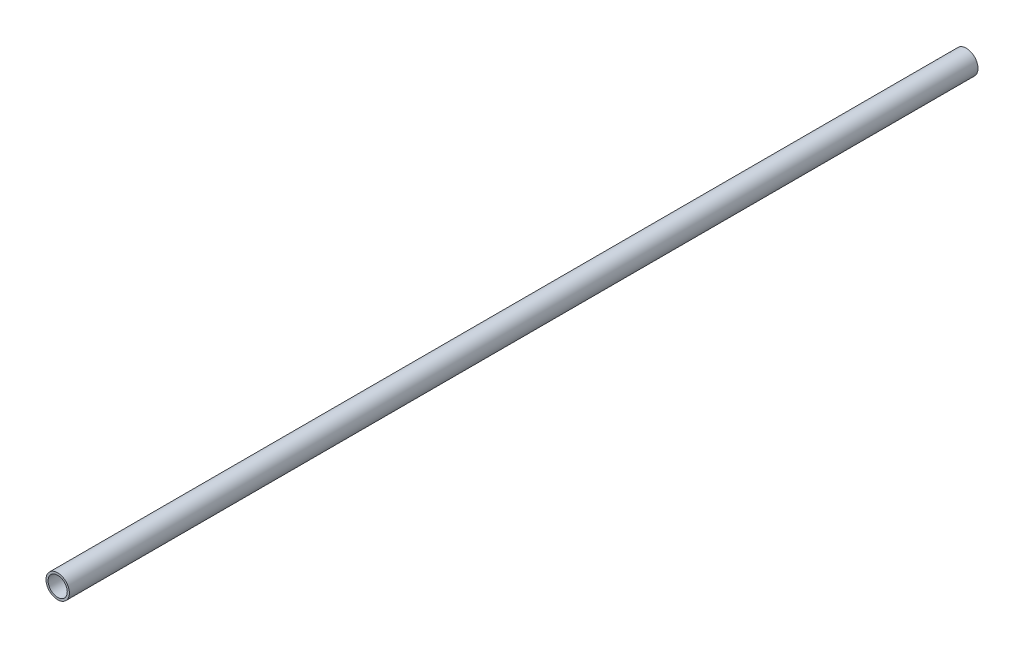
SolidWorks part; units mm, degrees
ref_plane "Front" through (0, 0, 0) normal (0, 0, 1) x (1, 0, 0)
ref_plane "Top" through (0, 0, 0) normal (0, 1, 0) x (1, 0, 0)
ref_plane "Side" through (0, 0, 0) normal (1, 0, 0) x (0, 0, -1)
sketch "PipeSketch" plane through (0, 0, 0) normal (0, 0, 1) x (1, 0, 0)
  circle A0 centre (0, 0) radius 70.612
  circle A1 centre (0, 0) radius 57.912
  dimension "OuterDiameter" = 141.224
  dimension "InnerDiameter" = 115.824
extrude "Extrusion" add sketch "PipeSketch" along normal blind 5486.4
sketch "FilterSketch" plane through (0, 0, 0) normal (0, 0, 1) x (1, 0, 0)
  circle A0 centre (0, 0) radius 63.5 construction
  dimension "NominalDiameter" = 127
